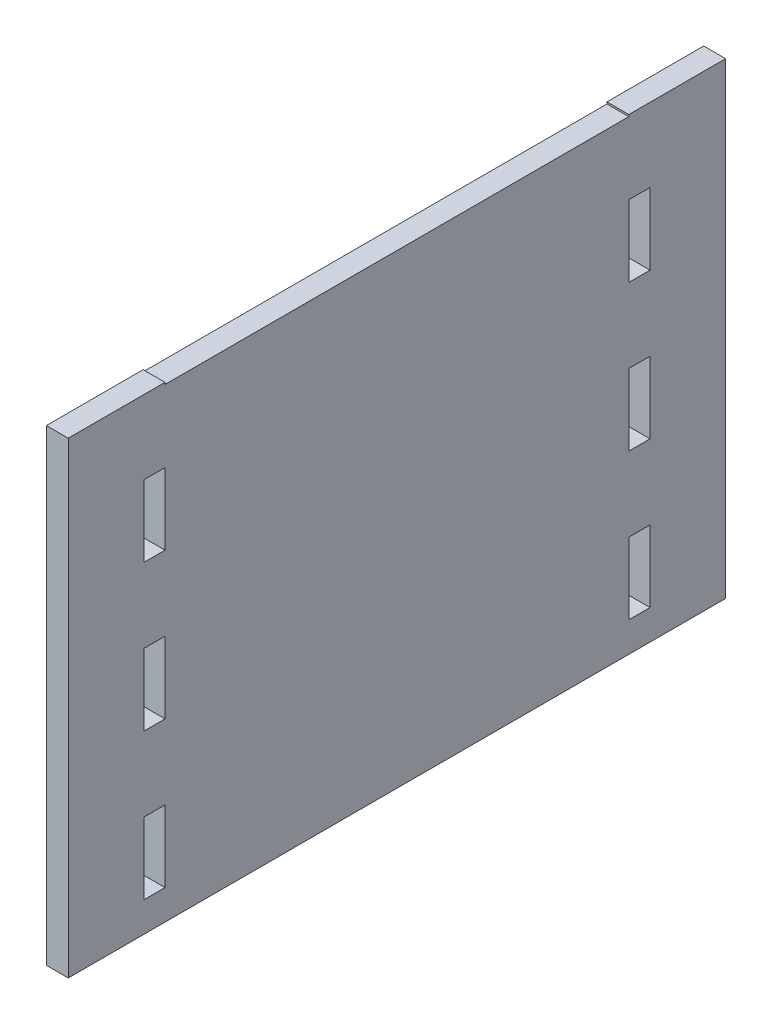
SolidWorks part; units mm, degrees
material "Acrylic (Medium-high impact)"
ref_plane "Front Plane" through (0, 0, 0) normal (0, 0, 1) x (1, 0, 0)
ref_plane "Top Plane" through (0, 0, 0) normal (0, 1, 0) x (1, 0, 0)
ref_plane "Right Plane" through (0, 0, 0) normal (1, 0, 0) x (0, 0, -1)
sketch "Sketch1" plane through (0, 0, 0) normal (1, 0, 0) x (0, 0, -1)
  line L1 (-31.75, -32) -> (31.75, -32) construction
  line L2 (-31.75, -32) -> (-31.75, 32) construction
  line L3 (-31.75, 32) -> (31.75, 32) construction
  line L4 (31.75, -32) -> (31.75, 32) construction
  line L5 (-31.75, -32) -> (31.75, 32) construction
  line L6 (-31.75, 32) -> (31.75, -32) construction
  line L7 (45, -32) -> (-45, -32)
  line L8 (45, -32) -> (45, 32)
  line L9 (45, 32) -> (-45, 32)
  line L10 (-45, -32) -> (-45, 32)
  line L11 (45, -32) -> (-45, 32) construction
  line L12 (45, 32) -> (-45, -32) construction
  point P0 (0, 0)
  point P6 (0, 0)
  dimension "D1" = 63.5
  dimension "D2" = 64
  dimension "D3" = 90
extrude "Boss-Extrude1" add sketch "Sketch1" along normal blind 3 contours L10 L9 L8 L7
sketch "Sketch2" plane through (3, 0, 0) normal (1, 0, 0) x (0, 0, -1)
  line L0 (31.75, -32) -> (31.75, 32) construction
  line L1 (-31.75, -32) -> (-31.75, 32) construction
  line L2 (31.75, -32) -> (31.75, 32) construction
  line L3 (-31.75, -32) -> (-31.75, 32) construction
  line L5 (-31.75, 21.9) -> (-34.65, 21.9)
  line L6 (-31.75, 21.9) -> (-31.75, 12.1)
  line L7 (-31.75, 12.1) -> (-34.65, 12.1)
  line L8 (-34.65, 21.9) -> (-34.65, 12.1)
  line L9 (45, 32) -> (-45, 32) construction
  line L10 (-31.75, 1.9) -> (-31.75, -7.9)
  line L11 (-31.75, 1.9) -> (-34.65, 1.9)
  line L12 (-34.65, 1.9) -> (-34.65, -7.9)
  line L13 (-31.75, -7.9) -> (-34.65, -7.9)
  line L14 (-31.75, -18.1) -> (-31.75, -27.9)
  line L15 (-31.75, -18.1) -> (-34.65, -18.1)
  line L16 (-34.65, -18.1) -> (-34.65, -27.9)
  line L17 (-31.75, -27.9) -> (-34.65, -27.9)
  line L18 (0, 0) -> (0, 32) construction
  line L19 (31.75, -18.1) -> (34.65, -18.1)
  line L20 (34.65, -18.1) -> (34.65, -27.9)
  line L21 (31.75, -27.9) -> (34.65, -27.9)
  line L22 (31.75, -18.1) -> (31.75, -27.9)
  line L23 (31.75, 1.9) -> (34.65, 1.9)
  line L24 (34.65, 1.9) -> (34.65, -7.9)
  line L25 (31.75, -7.9) -> (34.65, -7.9)
  line L26 (31.75, 1.9) -> (31.75, -7.9)
  line L27 (31.75, 12.1) -> (34.65, 12.1)
  line L28 (34.65, 21.9) -> (34.65, 12.1)
  line L29 (31.75, 21.9) -> (34.65, 21.9)
  line L30 (31.75, 21.9) -> (31.75, 12.1)
  dimension "D1" = 2.9
  dimension "D2" = 9.8
  dimension "D3" = 10.1
  dimension "D5" = 10.2
  dimension "D4" = 3
extrude "Cut-Extrude1" cut sketch "Sketch2" against normal blind 3
sketch "Sketch4" plane through (3, 0, 0) normal (1, 0, 0) x (0, 0, -1)
  line L0 (0, 0) -> (0, 31.875) construction
  line L1 (-31.75, 32) -> (31.75, 32)
  line L2 (-31.75, 32) -> (-31.75, 31.75)
  line L3 (-31.75, 31.75) -> (31.75, 31.75)
  line L4 (31.75, 32) -> (31.75, 31.75)
  line L5 (-31.75, 32) -> (31.75, 31.75) construction
  line L6 (-31.75, 31.75) -> (31.75, 32) construction
  line L7 (45, 32) -> (-45, 32) construction
  point P0 (0, 31.875)
  dimension "D1" = 63.5
  dimension "D2" = 0.25
extrude "Cut-Extrude2" cut sketch "Sketch4" against normal blind 10
